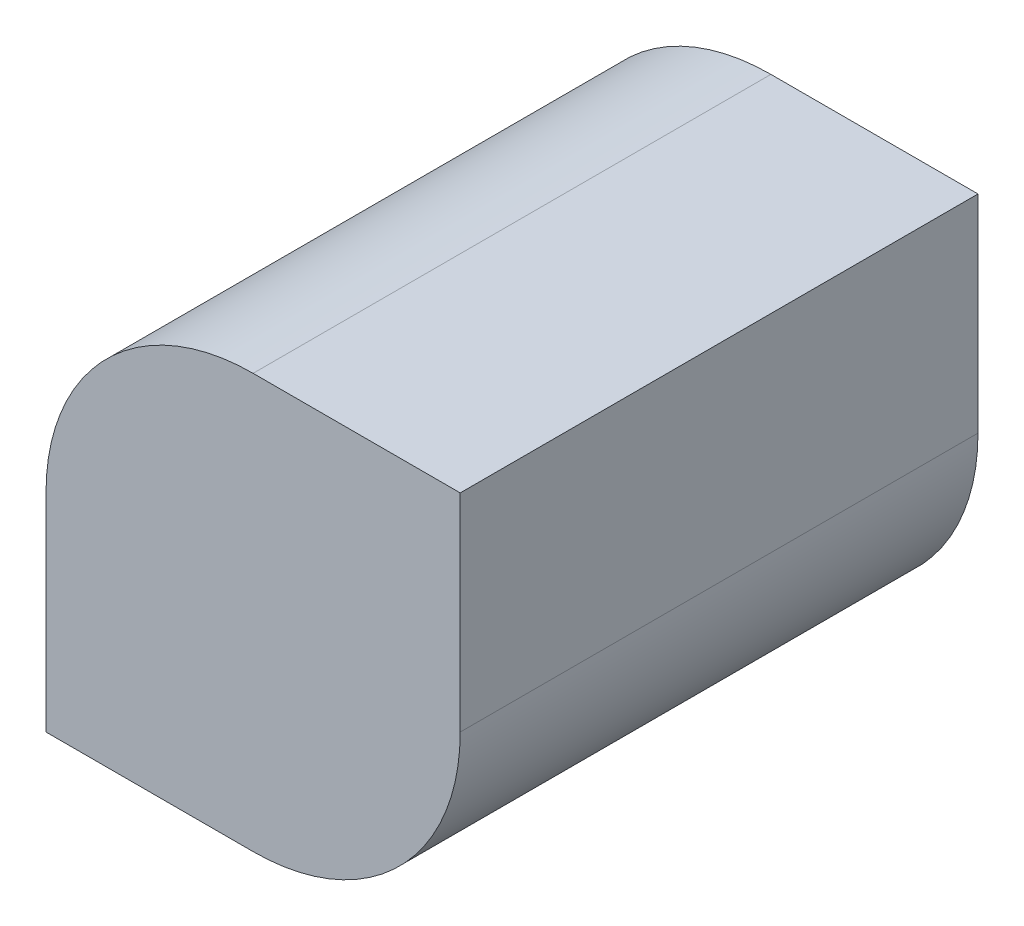
SolidWorks part; units mm, degrees
ref_plane "Front Plane" through (0, 0, 0) normal (0, 0, 1) x (1, 0, 0)
ref_plane "Top Plane" through (0, 0, 0) normal (0, 1, 0) x (1, 0, 0)
ref_plane "Right Plane" through (0, 0, 0) normal (1, 0, 0) x (0, 0, -1)
sketch "Sketch1" plane through (0, 0, 0) normal (0, 0, 1) x (1, 0, 0)
  line L0 (-10, 0) -> (0, 0)
  line L1 (10, 10) -> (10, 20)
  line L2 (10, 20) -> (0, 20)
  line L3 (-10, 10) -> (-10, 0)
  arc A0 (0, 0) -> (10, 10) centre (0, 10) ccw
  arc A1 (0, 20) -> (-10, 10) centre (0, 10) ccw
  dimension "D1" = 10
  dimension "D2" = 10
  dimension "D3" = 10
  dimension "D4" = 10
extrude "Boss-Extrude1" add sketch "Sketch1" along normal blind 25
